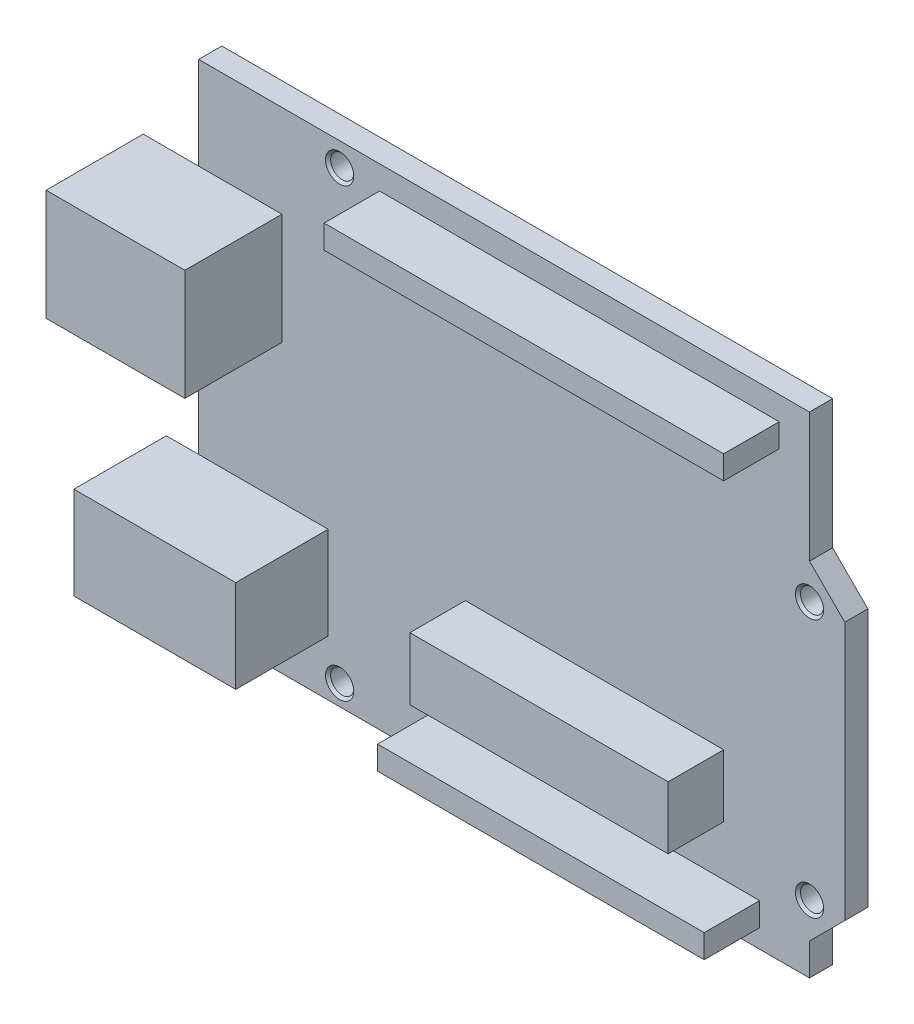
SolidWorks part; units mm, degrees
ref_plane "前视基准面" through (0, 0, 0) normal (0, 0, 1) x (1, 0, 0)
ref_plane "上视基准面" through (0, 0, 0) normal (0, 1, 0) x (1, 0, 0)
ref_plane "右视基准面" through (0, 0, 0) normal (1, 0, 0) x (0, 0, -1)
sketch "草图1" plane through (0, 0, 0) normal (0, 0, 1) x (1, 0, 0)
  line L0 (-35.4452, 28.5367) -> (-35.4452, -24.4633)
  line L1 (-35.4452, -24.4633) -> (30.5948, -24.4633)
  line L6 (30.5948, 28.5367) -> (-35.4452, 28.5367)
  line L8 (30.5948, 28.5367) -> (30.5948, 14.5713)
  line L9 (30.5948, 14.5713) -> (34.4093, 10.7567)
  line L10 (34.4093, 10.7567) -> (34.4093, -17.1833)
  line L11 (34.4093, -17.1833) -> (30.5948, -20.9979)
  line L12 (30.5948, -20.9979) -> (30.5948, -24.4633)
  point P5 (-20.2052, 25.9967)
  point P9 (-20.2052, -22.2633)
  point P10 (30.5948, -17.1833)
  point P11 (30.5948, 10.7567)
  dimension "D1" = 53
  dimension "D2" = 66.04
  dimension "D3" = 17.78
  dimension "D4" = 45.72
  dimension "D5" = 50.8
  dimension "D6" = 15.24
  dimension "D7" = 15.24
  dimension "D8" = 2.54
  dimension "D9" = 66.04
  dimension "D10" = 66.04
extrude "凸台-拉伸1" add sketch "草图1" along normal blind 2.5
sketch "草图2" plane through (0, 0, 0) normal (0, 0, 1) x (1, 0, 0)
  line L0 (-35.4452, 28.5367) -> (-35.4452, -24.4633)
  line L1 (-35.4452, -24.4633) -> (30.5948, -24.4633)
  line L6 (30.5948, 28.5367) -> (-35.4452, 28.5367)
  line L8 (30.5948, 28.5367) -> (30.5948, 14.5713)
  line L9 (30.5948, 14.5713) -> (34.4093, 10.7567)
  line L10 (34.4093, 10.7567) -> (34.4093, -17.1833)
  line L11 (34.4093, -17.1833) -> (30.5948, -20.9979)
  line L12 (30.5948, -20.9979) -> (30.5948, -24.4633)
  point P5 (-20.2052, 25.9967)
  point P9 (-20.2052, -22.2633)
  point P10 (30.5948, -17.1833)
  point P11 (30.5948, 10.7567)
  dimension "D1" = 53
  dimension "D2" = 66.04
  dimension "D3" = 17.78
  dimension "D4" = 45.72
  dimension "D5" = 50.8
  dimension "D6" = 15.24
  dimension "D7" = 15.24
  dimension "D8" = 2.54
  dimension "D9" = 66.04
  dimension "D10" = 66.04
hole_wizard "M3 螺纹孔1" positions "草图5" profile "草图6" tap size "M3" standard "GB" end condition through all
sketch "草图5" plane through (0, 0, 2.5) normal (0, 0, 1) x (1, 0, 0)
  point P0 (-20.2052, 25.9967)
  point P3 (30.5948, 10.7567)
  point P6 (30.5948, -17.1833)
  point P9 (-20.2052, -22.2633)
sketch "草图6" plane through (-20.2052, 25.9967, 2.5) normal (1, 0, 0) x (0, -1, 0)
  line L0 (0, 0) -> (0, 2.5)
  line L1 (0, 2.5) -> (1.25, 2.5)
  line L2 (1.25, 2.5) -> (1.25, 0.275)
  line L3 (1.25, 0.275) -> (1.525, 0)
  line L5 (1.525, 0) -> (0, 0)
  line L6 (-1.25, 0.275) -> (-1.525, 0) construction
  line L11 (0, -6.35) -> (0, 107.95) construction
  dimension "通孔螺纹孔钻头直径" = 2.5
  dimension "通孔螺纹孔钻头深度" = 2.5
  dimension "近端锥形沉头孔直径" = 3.05
  dimension "近端锥形沉头孔角度" = 90
cosmetic thread "孔螺蚊线1" parameters "D2"=3
cosmetic thread "孔螺蚊线2" parameters "D2"=3
cosmetic thread "孔螺蚊线3" parameters "D2"=3
cosmetic thread "孔螺蚊线4" parameters "D2"=3
sketch "草图8" plane through (0, 0, 2.5) normal (0, 0, 1) x (1, 0, 0)
  line L1 (-6.6105, -7.7302) -> (21.3144, -7.7302)
  line L2 (-6.6105, -7.7302) -> (-6.6105, -14.4779)
  line L3 (-6.6105, -14.4779) -> (21.3144, -14.4779)
  line L4 (21.3144, -7.7302) -> (21.3144, -14.4779)
  line L5 (-10.099, -19.9096) -> (25.2083, -19.9096)
  line L6 (-10.099, -19.9096) -> (-10.099, -22.4489)
  line L7 (-10.099, -22.4489) -> (25.2083, -22.4489)
  line L8 (25.2083, -19.9096) -> (25.2083, -22.4489)
  line L9 (-15.8918, 25.983) -> (27.3149, 25.983)
  line L10 (-15.8918, 25.983) -> (-15.8918, 23.4438)
  line L11 (-15.8918, 23.4438) -> (27.3149, 23.4438)
  line L12 (27.3149, 25.983) -> (27.3149, 23.4438)
extrude "凸台-拉伸2" add sketch "草图8" along normal blind 6
sketch "草图9" plane through (0, 0, 2.5) normal (0, 0, 1) x (1, 0, 0)
  line L0 (-35.4452, 28.5367) -> (-35.4452, -24.4633) construction
  line L1 (-41.4452, 18.5367) -> (-26.4452, 18.5367)
  line L2 (-41.4452, 18.5367) -> (-41.4452, 6.5367)
  line L3 (-41.4452, 6.5367) -> (-26.4452, 6.5367)
  line L4 (-26.4452, 18.5367) -> (-26.4452, 6.5367)
  line L5 (30.5948, 28.5367) -> (-35.4452, 28.5367) construction
  dimension "D1" = 15
  dimension "D2" = 12
  dimension "D3" = 9
  dimension "D4" = 10
extrude "凸台-拉伸3" add sketch "草图9" along normal blind 10.5
sketch "草图10" plane through (-41.4452, 0, 0) normal (-1, 0, 0) x (0, 0, 1)
  line L0 (2.5, 12.5367) -> (13, 12.5367) construction
  line L1 (2.5, 18.5367) -> (2.5, 6.5367) construction
  line L2 (13, 18.5367) -> (13, 6.5367) construction
  line L3 (3.5, 17.3448) -> (3.5, 7.7286)
  line L4 (3.5, 17.3448) -> (9.3233, 17.3448)
  line L5 (9.3233, 17.3448) -> (12, 15.4526)
  line L6 (12, 15.4526) -> (12, 9.707)
  line L7 (12, 9.707) -> (9.3233, 7.7286)
  line L8 (3.5, 7.7286) -> (9.3233, 7.7286)
  line L10 (6.234, 15.1068) -> (8.7817, 15.1068)
  line L11 (6.234, 15.1068) -> (6.234, 9.9666)
  line L12 (6.234, 9.9666) -> (8.7817, 9.9666)
  line L13 (8.7817, 15.1068) -> (8.7817, 9.9666)
  dimension "D1" = 1
  dimension "D2" = 1
extrude "切除-拉伸1" cut sketch "草图10" against normal blind 10.5
sketch "草图12" plane through (0, 0, 2.5) normal (0, 0, 1) x (1, 0, 0)
  line L0 (-35.4452, -18.4633) -> (-35.4452, -8.4633)
  line L1 (-35.4452, 28.5367) -> (-35.4452, -24.4633) construction
  line L2 (-35.4452, -8.4633) -> (-21.4452, -8.4633)
  line L3 (-21.4452, -8.4633) -> (-21.4452, -18.4633)
  line L4 (-21.4452, -18.4633) -> (-35.4452, -18.4633)
  line L5 (-35.4452, -24.4633) -> (30.5948, -24.4633) construction
  dimension "D1" = 6
  dimension "D2" = 10
  dimension "D3" = 14
extrude "凸台-拉伸4" add sketch "草图12" along normal blind 10
sketch "草图13" plane through (-35.4452, 0, 0) normal (-1, 0, 0) x (0, 0, 1)
  line L0 (2.5, -8.4633) -> (12.5, -18.4633) construction
  line L1 (12.5, -18.4633) -> (2.5, -18.4633) construction
  line L2 (12.5, -8.4633) -> (12.5, -18.4633) construction
  line L3 (12.5, -8.4633) -> (2.5, -18.4633) construction
  line L4 (12.5, -8.4633) -> (2.5, -8.4633) construction
  line L5 (2.5, -8.4633) -> (2.5, -18.4633)
  line L6 (2.5, -18.4633) -> (12.5, -18.4633)
  line L7 (12.5, -18.4633) -> (12.5, -8.4633)
  line L8 (12.5, -8.4633) -> (2.5, -8.4633)
  circle A0 centre (7.5, -13.4633) radius 2.75
  dimension "D1" = 5.5
extrude "凸台-拉伸5" add sketch "草图13" along normal blind 3.5
sketch "草图14" plane through (-35.4452, 0, 0) normal (-1, 0, 0) x (0, 0, 1)
  circle A1 centre (7.5, -13.4633) radius 2.75
  circle A2 centre (7.5, -13.4633) radius 2.75
  dimension "D1" = 0
extrude "切除-拉伸3" cut sketch "草图14" against normal blind 8
equation "\"3.510.00mm\"=10"
